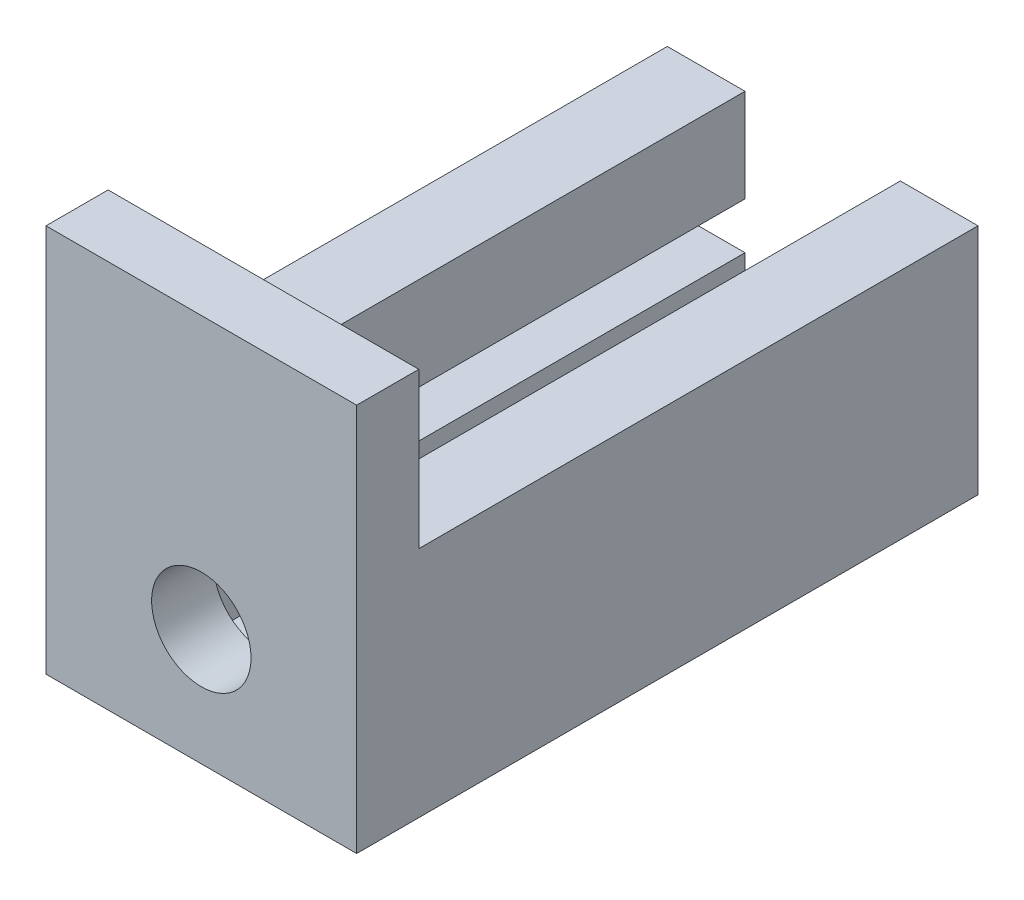
SolidWorks part; units mm, degrees
ref_plane "Plan de face" through (0, 0, 0) normal (0, 0, 1) x (1, 0, 0)
ref_plane "Plan de dessus" through (0, 0, 0) normal (0, 1, 0) x (1, 0, 0)
ref_plane "Plan de droite" through (0, 0, 0) normal (1, 0, 0) x (0, 0, -1)
sketch "Esquisse1" plane through (0, 0, 0) normal (0, 0, 1) x (1, 0, 0)
  line L0 (0, 0) -> (-5, 0)
  line L1 (-5, 0) -> (-5, 15)
  line L2 (-5, 15) -> (0, 15)
  line L3 (0, 15) -> (0, 9)
  line L4 (0, 9) -> (-3, 9)
  line L5 (-3, 9) -> (-3, 6)
  line L6 (-3, 6) -> (0, 6)
  line L8 (10, 6) -> (10, 2)
  line L9 (10, 2) -> (0, 2)
  line L11 (10, 0) -> (15, 0)
  line L12 (15, 0) -> (15, 15)
  line L13 (15, 15) -> (10, 15)
  line L14 (10, 15) -> (10, 9)
  line L15 (10, 9) -> (13, 9)
  line L16 (13, 9) -> (13, 6)
  line L17 (13, 6) -> (10, 6)
  line L19 (0, 2) -> (0, 6)
  line L21 (0, 0) -> (10, 0)
  dimension "D1" = 15
  dimension "D2" = 5
  dimension "D3" = 3
  dimension "D4" = 3
  dimension "D5" = 6
  dimension "D6" = 6
  dimension "D7" = 4
  dimension "D8" = 10
  dimension "D9" = 5
  dimension "D10" = 3
  dimension "D11" = 3
  dimension "D12" = 15
  dimension "D13" = 5
  dimension "D14" = 3
  dimension "D15" = 6
  dimension "D16" = 2
extrude "Boss.-Extru.1" add sketch "Esquisse1" along normal blind 36
sketch "Esquisse2" plane through (0, 0, 36) normal (0, 0, 1) x (1, 0, 0)
  line L1 (-5, 15) -> (15, 15)
  line L2 (-5, 15) -> (-5, 0)
  line L3 (-5, 0) -> (15, 0)
  line L4 (15, 15) -> (15, 0)
extrude "Boss.-Extru.2" add sketch "Esquisse2" along normal blind 4
sketch "Esquisse3" plane through (0, 0, 40) normal (0, 0, 1) x (1, 0, 0)
  line L0 (5, 15) -> (5, 0) construction
  line L1 (15, 15) -> (-5, 15) construction
  line L2 (-5, 0) -> (15, 0) construction
  line L3 (15, 7.5) -> (-5, 7.5) construction
  line L4 (15, 0) -> (15, 15) construction
  line L5 (-5, 15) -> (-5, 0) construction
  circle A0 centre (5, 7.5) radius 3.2
extrude "Enlèv. mat.-Extru.1" cut sketch "Esquisse3" against normal blind 4
sketch "Esquisse4" plane through (0, 15, 0) normal (0, 1, 0) x (1, 0, 0)
  line L0 (-5, -40) -> (-5, 0) construction
  line L1 (-5, -36) -> (15, -36)
  line L2 (-5, -36) -> (-5, -40)
  line L3 (-5, -40) -> (15, -40)
  line L4 (15, -36) -> (15, -40)
extrude "Boss.-Extru.3" add sketch "Esquisse4" along normal blind 10
sketch "Esquisse5" plane through (0, 0, 36) normal (0, 0, -1) x (-1, 0, 0)
  line L0 (-5, 2) -> (-5, 7.5) construction
  line L1 (-10, 2) -> (0, 2) construction
  dimension "D1" = 5.5
